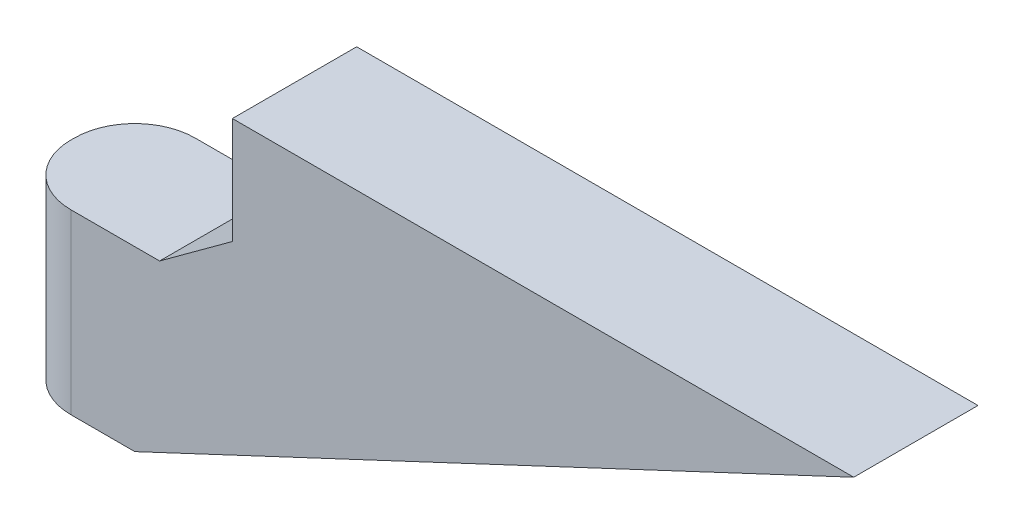
SolidWorks part; units mm, degrees
ref_plane "Front Plane" through (0, 0, 0) normal (0, 0, 1) x (1, 0, 0)
ref_plane "Top Plane" through (0, 0, 0) normal (0, 1, 0) x (1, 0, 0)
ref_plane "Right Plane" through (0, 0, 0) normal (1, 0, 0) x (0, 0, -1)
sketch "Sketch1" plane through (0, 0, 0) normal (0, 0, 1) x (1, 0, 0)
  line L0 (-30.1625, 0.635) -> (-19.4945, 0.635)
  line L1 (30.1625, 12.065) -> (-30.1625, 12.065)
  line L2 (30.1625, 12.065) -> (30.1625, -12.065)
  line L3 (30.1625, -12.065) -> (-30.1625, -12.065)
  line L4 (-30.1625, 12.065) -> (-30.1625, -12.065)
  line L5 (30.1625, 12.065) -> (-30.1625, -12.065) construction
  line L6 (30.1625, -12.065) -> (-30.1625, 12.065) construction
  line L7 (-14.2875, 12.065) -> (-14.2875, 4.445)
  line L8 (-14.2875, 4.445) -> (-19.4945, 0.635)
  line L9 (-14.2875, 4.445) -> (-14.2875, -12.065) construction
  line L10 (-21.2725, -12.065) -> (30.1625, 12.065)
  point P0 (0, 0)
  point P6 (-30.1625, 0.635)
  point P9 (-14.2875, 12.065)
  point P12 (-21.2725, -12.065)
  dimension "D1" = 24.13
  dimension "D2" = 60.325
  dimension "D3" = 12.7
  dimension "D4" = 10.668
  dimension "D5" = 15.875
  dimension "D6" = 8.89
  dimension "D7" = 7.62
extrude "Boss-Extrude1" add sketch "Sketch1" along normal blind 8.89 contours L3 L10 L1 L7 L8 L0 L4
fillet "Fillet1" radius 4.318 2 edges at (-30.1625, -5.715, 0) (-30.1625, -5.715, 8.89)
